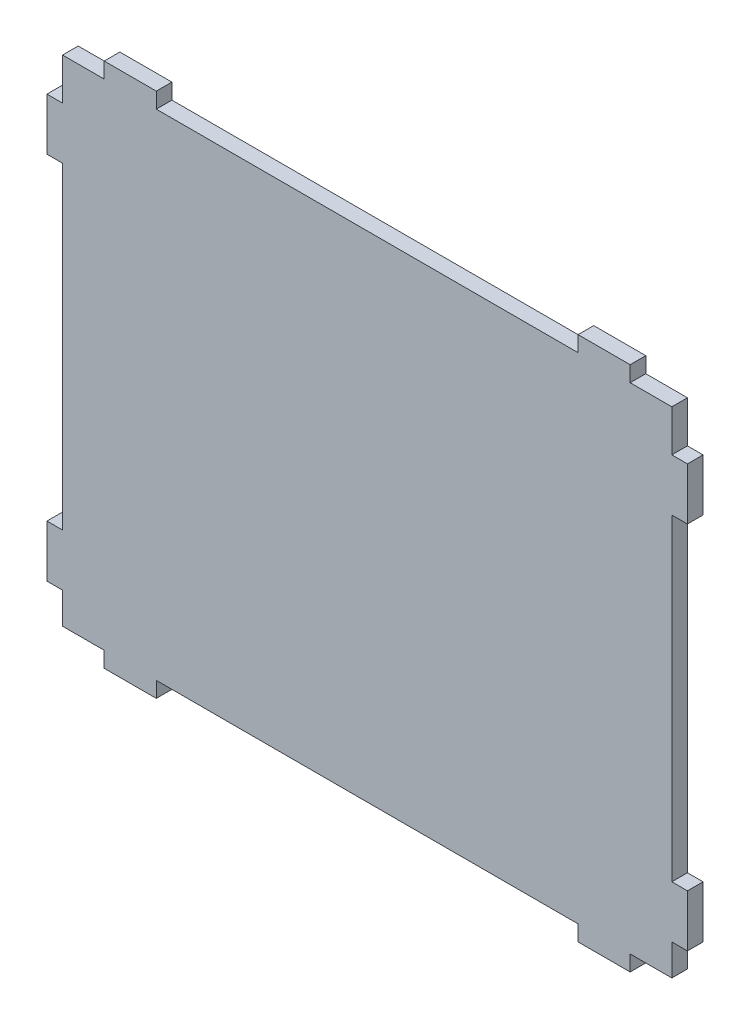
SolidWorks part; units mm, degrees
ref_plane "Alzado" through (0, 0, 0) normal (0, 0, 1) x (1, 0, 0)
ref_plane "Planta" through (0, 0, 0) normal (0, 1, 0) x (1, 0, 0)
ref_plane "Vista lateral" through (0, 0, 0) normal (1, 0, 0) x (0, 0, -1)
sketch "Croquis1" plane through (0, 0, 0) normal (0, 0, 1) x (1, 0, 0)
  line L0 (-50.8303, 36.2788) -> (-42.8303, 36.2788)
  line L1 (-50.8303, 36.2788) -> (66.1697, 36.2788) construction
  line L2 (-50.8303, 36.2788) -> (-50.8303, -58.7212) construction
  line L3 (-50.8303, -58.7212) -> (66.1697, -58.7212) construction
  line L4 (66.1697, 36.2788) -> (66.1697, -58.7212) construction
  line L5 (-42.8303, 36.2788) -> (-42.8303, 39.2788)
  line L6 (-42.8303, 39.2788) -> (-32.8303, 39.2788)
  line L7 (-32.8303, 39.2788) -> (-32.8303, 36.2788)
  line L8 (-32.8303, 36.2788) -> (48.1697, 36.2788)
  line L9 (48.1697, 36.2788) -> (48.1697, 39.2788)
  line L10 (48.1697, 39.2788) -> (58.1697, 39.2788)
  line L11 (58.1697, 39.2788) -> (58.1697, 36.2788)
  line L12 (58.1697, 36.2788) -> (66.1697, 36.2788)
  line L13 (-50.8303, -11.2212) -> (66.1697, -11.2212) construction
  line L14 (58.1697, -58.7212) -> (66.1697, -58.7212)
  line L15 (58.1697, -61.7212) -> (58.1697, -58.7212)
  line L16 (48.1697, -61.7212) -> (58.1697, -61.7212)
  line L17 (48.1697, -58.7212) -> (48.1697, -61.7212)
  line L18 (-32.8303, -58.7212) -> (48.1697, -58.7212)
  line L19 (-32.8303, -61.7212) -> (-32.8303, -58.7212)
  line L20 (-42.8303, -61.7212) -> (-32.8303, -61.7212)
  line L21 (-42.8303, -58.7212) -> (-42.8303, -61.7212)
  line L22 (-50.8303, -58.7212) -> (-42.8303, -58.7212)
  line L23 (-50.8303, -58.7212) -> (-50.8303, -52.7212)
  line L24 (-50.8303, -52.7212) -> (-53.8303, -52.7212)
  line L25 (-53.8303, -52.7212) -> (-53.8303, -42.7212)
  line L26 (-53.8303, -42.7212) -> (-50.8303, -42.7212)
  line L27 (-50.8303, -42.7212) -> (-50.8303, 18.2788)
  line L28 (-50.8303, 18.2788) -> (-53.8303, 18.2788)
  line L29 (-53.8303, 18.2788) -> (-53.8303, 28.2788)
  line L30 (-53.8303, 28.2788) -> (-50.8303, 28.2788)
  line L31 (-50.8303, 28.2788) -> (-50.8303, 36.2788)
  line L32 (7.6697, -11.2212) -> (7.6697, -58.7212) construction
  line L33 (66.1697, 28.2788) -> (66.1697, 36.2788)
  line L34 (69.1697, 28.2788) -> (66.1697, 28.2788)
  line L35 (69.1697, 18.2788) -> (69.1697, 28.2788)
  line L36 (66.1697, 18.2788) -> (69.1697, 18.2788)
  line L37 (66.1697, -42.7212) -> (66.1697, 18.2788)
  line L38 (69.1697, -42.7212) -> (66.1697, -42.7212)
  line L39 (69.1697, -52.7212) -> (69.1697, -42.7212)
  line L40 (66.1697, -52.7212) -> (69.1697, -52.7212)
  line L41 (66.1697, -58.7212) -> (66.1697, -52.7212)
  dimension "D1" = 117
  dimension "D2" = 95
  dimension "D3" = 8
  dimension "D4" = 3
  dimension "D6" = 10
  dimension "D7" = 10
  dimension "D8" = 8
  dimension "D9" = 6
  dimension "D10" = 10
  dimension "D11" = 3
  dimension "D13" = 10
  dimension "D14" = 8
extrude "Saliente-Extruir1" add sketch "Croquis1" along normal blind 3
